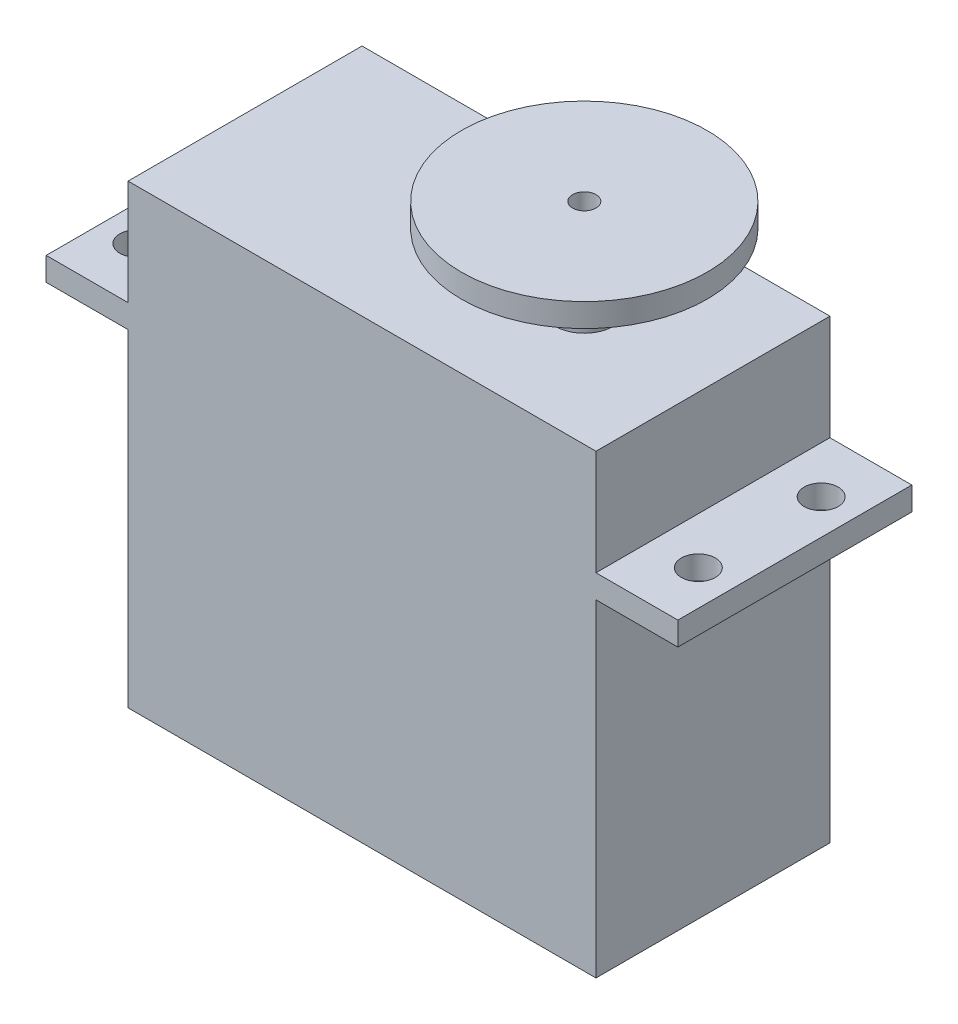
SolidWorks part; units mm, degrees
ref_plane "Front Plane" through (0, 0, 0) normal (0, 0, 1) x (1, 0, 0)
ref_plane "Top Plane" through (0, 0, 0) normal (0, 1, 0) x (1, 0, 0)
ref_plane "Right Plane" through (0, 0, 0) normal (1, 0, 0) x (0, 0, -1)
sketch "Sketch1" plane through (0, 0, 0) normal (0, 1, 0) x (1, 0, 0)
  line L1 (-20, -10) -> (20, -10)
  line L2 (-20, -10) -> (-20, 10)
  line L3 (-20, 10) -> (20, 10)
  line L4 (20, -10) -> (20, 10)
  line L5 (-20, -10) -> (20, 10) construction
  line L6 (-20, 10) -> (20, -10) construction
  point P0 (0, 0)
  dimension "D1" = 40
  dimension "D2" = 20
extrude "Boss-Extrude1" add sketch "Sketch1" along normal blind 39
sketch "Sketch2" plane through (20, 0, 0) normal (1, 0, 0) x (0, 0, -1)
  line L0 (-10, 39) -> (-10, 0) construction
  line L1 (-10, 30) -> (10, 30)
  line L2 (-10, 30) -> (-10, 28)
  line L3 (-10, 28) -> (10, 28)
  line L4 (10, 30) -> (10, 28)
  line L5 (10, 39) -> (10, 0) construction
  line L6 (-10, 39) -> (10, 39) construction
  dimension "D1" = 2
  dimension "D2" = 9
extrude "Boss-Extrude2" add sketch "Sketch2" along normal blind 7
sketch "Sketch3" plane through (-20, 0, 0) normal (-1, 0, 0) x (0, 0, 1)
  line L0 (-10, 39) -> (-10, 0) construction
  line L1 (-10, 30) -> (10, 30)
  line L2 (-10, 30) -> (-10, 28)
  line L3 (-10, 28) -> (10, 28)
  line L4 (10, 30) -> (10, 28)
  line L5 (10, 39) -> (10, 0) construction
  point P10 (-33.3811, 39.2132)
  dimension "D1" = 20
  dimension "D2" = 2
  dimension "D3" = 9
extrude "Boss-Extrude3" add sketch "Sketch3" along normal blind 7
sketch "Sketch4" plane through (0, 30, 0) normal (0, 1, 0) x (1, 0, 0)
  line L0 (27, 10) -> (20, 10) construction
  line L1 (20, 10) -> (20, -10) construction
  line L2 (27, -10) -> (20, -10) construction
  line L3 (-20, -10) -> (-20, 10) construction
  line L4 (-27, 10) -> (-20, 10) construction
  line L5 (-27, -10) -> (-20, -10) construction
  circle A0 centre (24, 5.25) radius 1.45
  circle A1 centre (24, -5.25) radius 1.45
  circle A2 centre (-24, 5.25) radius 1.45
  circle A3 centre (-24, -5.25) radius 1.45
  point P18 (0, 0)
  dimension "D5" = 2.9
  dimension "D6" = 2.9
  dimension "D7" = 2.9
  dimension "D8" = 2.9
  dimension "D1" = 4.75
  dimension "D2" = 4
  dimension "D3" = 4
  dimension "D4" = 4.75
  dimension "D9" = 4
  dimension "D10" = 4.75
  dimension "D11" = 4.75
  dimension "D12" = 4
extrude "Cut-Extrude1" cut sketch "Sketch4" against normal through all
sketch "Sketch5" plane through (0, 39, 0) normal (0, 1, 0) x (1, 0, 0)
  line L0 (20, -10) -> (20, 10) construction
  circle A0 centre (9, 0) radius 2.5
  dimension "D1" = 5
  dimension "D2" = 11
extrude "Boss-Extrude4" add sketch "Sketch5" along normal blind 6
sketch "Sketch6" plane through (0, 45, 0) normal (0, 1, 0) x (1, 0, 0)
  circle A0 centre (9, 0) radius 10.5
  dimension "D1" = 21
extrude "Boss-Extrude5" add sketch "Sketch6" along normal blind 2
sketch "Sketch7" plane through (0, 47, 0) normal (0, 1, 0) x (1, 0, 0)
  circle A0 centre (9, 0) radius 1
  dimension "D1" = 2
extrude "Cut-Extrude3" cut sketch "Sketch7" against normal blind 6
